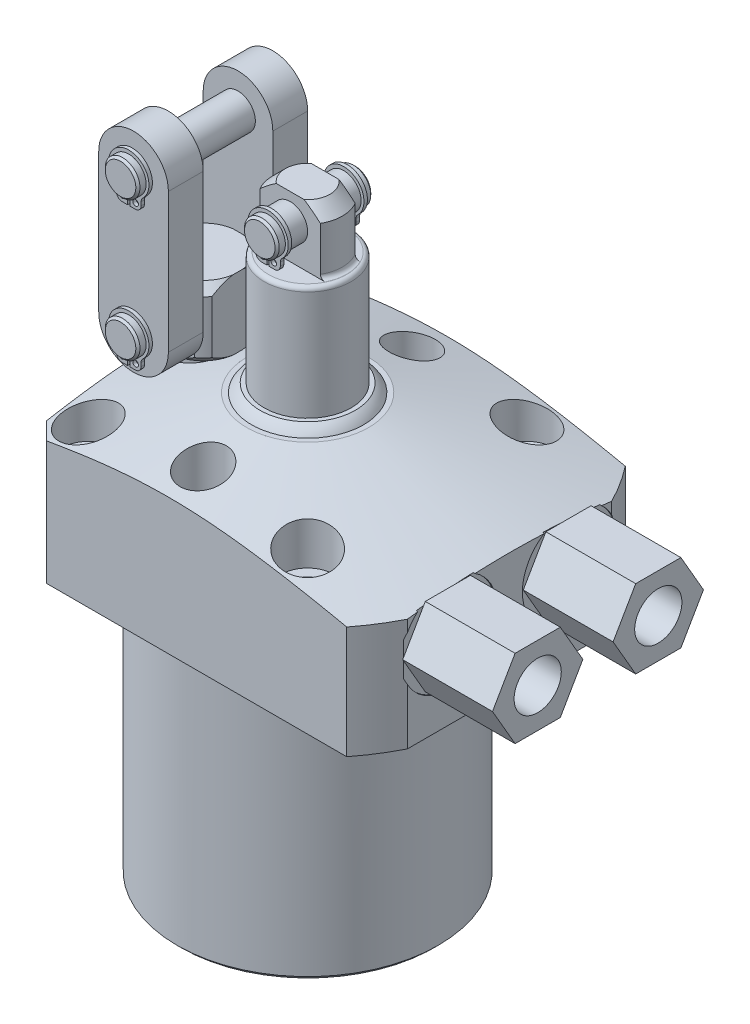
SolidWorks part; units mm, degrees
material "Alloy Steel"
ref_plane "Front Plane" through (0, 0, 0) normal (0, 0, 1) x (1, 0, 0)
ref_plane "Top Plane" through (0, 0, 0) normal (0, 1, 0) x (1, 0, 0)
ref_plane "Right Plane" through (0, 0, 0) normal (1, 0, 0) x (0, 0, -1)
sketch "Sketch28" plane through (0, 0, 0) normal (0, 0, 1) x (1, 0, 0)
  line L0 (0, 0) -> (0, 146.1857) construction
  line L1 (-11.1125, 28.575) -> (-41.275, 20.493)
  line L2 (-41.275, 20.493) -> (-41.275, 0)
  line L3 (-41.275, 0) -> (-23.8125, 0)
  line L6 (-23.8125, 0) -> (-23.8125, -47.625)
  line L9 (-23.8125, -47.625) -> (0, -47.625)
  line L10 (0, -47.625) -> (0, 28.575)
  line L11 (0, 28.575) -> (-11.1125, 28.575)
  dimension "D2" = 47.625
  dimension "D3" = 47.625
  dimension "D5" = 82.55
  dimension "D6" = 15
  dimension "D7" = 22.225
  dimension "D8" = 28.575
revolve "Revolve7" add sketch "Sketch28" angle 360 about L0
sketch "Sketch3" plane through (0, 28.575, 0) normal (0, 1, 0) x (-1, 0, 0)
  line L0 (25.4, -25.4) -> (-36.83, -25.4)
  line L3 (-36.83, 25.4) -> (25.4, 25.4)
  line L4 (25.4, -25.4) -> (25.4, 25.4)
  line L5 (-36.83, -25.4) -> (-36.83, 25.4)
  line L6 (-29.7523, 0) -> (31.3525, 0) construction
  dimension "D1" = 50.8
  dimension "D2" = 36.83
  dimension "D5" = 25.4
extrude "Cut-Extrude9" cut sketch "Sketch3" against normal up to next (76.2 mm away) flip side to cut
chamfer "Chamfer8" distance 3.175 angle 45 2 edges at (-25.4, 10.9638, -25.4) (-25.4, 10.9638, 25.4)
chamfer "Chamfer5" distance 0.762 angle 45 1 edges at (0, -47.625, -23.8125)
hole_wizard "Hole1" positions "Sketch32" profile "Sketch31" legacy
sketch "Sketch32" plane through (0, 28.575, 0) normal (0, 1, 0) x (-1, 0, 0)
  line L1 (0, 0) -> (-56.2722, 0) construction
  line L2 (0, 0) -> (0, 46.6984) construction
  point P11 (-20.0025, -20.0025)
  point P23 (-20.0025, 20.0025)
  point P25 (20.0025, -20.0025)
  point P26 (20.0025, 20.0025)
  dimension "D1" = 40.005
  dimension "D2" = 40.005
sketch "Sketch31" plane through (20.0025, 28.575, -20.0025) normal (1, 0, 0) x (0, 0, 1)
  line L0 (0, 0) -> (0, 28.575)
  line L1 (0, 28.575) -> (2.7813, 28.575)
  line L2 (2.7813, 28.575) -> (2.7813, 11.0998)
  line L3 (2.7813, 11.0998) -> (4.7625, 11.0998)
  line L4 (4.7625, 11.0998) -> (4.7625, 0)
  line L5 (4.7625, 0) -> (0, 0)
  line L6 (0, 110) -> (0, -10) construction
  dimension "Diameter" = 5.5626
  dimension "Depth" = 28.575
  dimension "C-Bore Diameter" = 9.525
  dimension "C-Bore Depth" = 11.0998
sketch "Sketch34" plane through (0, 28.575, 0) normal (0, 1, 0) x (1, 0, 0)
  line L0 (0, 0) -> (-28.6526, 0) construction
  circle A0 centre (0, 19.05) radius 4.2164
  circle A1 centre (0, -19.05) radius 4.2164
  circle A2 centre (0, 0) radius 19.05 construction
  circle A3 centre (-19.05, 0) radius 4.2164
  dimension "D1" = 8.4328
  dimension "D2" = 19.05
extrude "Cut-Extrude10" cut sketch "Sketch34" against normal blind 12.7
ref_plane "Plane23" through (0, 14.2748, 0) normal (0, -1, 0) x (1, 0, 0)
sketch "S2D0007" plane through (0, 14.2748, 0) normal (0, -1, 0) x (1, 0, 0)
  line L0 (36.83, -10.9982) -> (36.83, -19.6596)
  line L1 (36.83, -19.6596) -> (36.576, -19.6596)
  line L2 (36.576, -19.6596) -> (36.576, -15.5765)
  line L3 (36.576, -15.5765) -> (34.5059, -15.1365)
  line L4 (34.5059, -15.1365) -> (33.822, -14.4526)
  line L5 (33.822, -14.4526) -> (24.384, -14.4526)
  line L6 (24.384, -14.4526) -> (22.3084, -10.9982)
  line L7 (22.3084, -10.9982) -> (36.83, -10.9982)
  line L8 (-11.7468, -10.9982) -> (-12.1894, -10.9982) construction
  line L10 (36.83, -18.6327) -> (36.83, 18.6327) construction
  dimension "D1" = 9.1567
  dimension "D2" = 59
  dimension "D3" = 6.9088
  dimension "D4" = 45
  dimension "D5" = 12
  dimension "D6" = 2.0701
  dimension "D7" = 0.254
  dimension "D8" = 17.3228
  dimension "D9" = 10.9982
  dimension "D10" = 12.192
revolve "Cut-Revolve2" cut sketch "S2D0007" angle 360 about L8
ref_plane "Plane24" through (0, 0, -10.9982) normal (0, 0, 1) x (1, 0, 0)
sketch "Sketch6" plane through (0, 0, -10.9982) normal (0, 0, 1) x (1, 0, 0)
  line L0 (32.5341, 0) -> (-22.225, 0) construction
  line L1 (35.668, 0) -> (35.668, 1.4478)
  line L2 (35.668, 1.4478) -> (32.6075, 1.4478)
  line L3 (32.5341, 0) -> (36.83, 0) construction
  line L5 (29.9974, 0.5588) -> (31.1404, 0.5588)
  line L6 (29.9974, 0) -> (35.668, 0)
  line L8 (29.9974, 0.5588) -> (29.9974, 0)
  line L9 (29.9974, -21.0492) -> (29.9974, 0.6686) construction
  arc A1 (31.1404, 0.5588) -> (32.6075, 1.4478) centre (29.9974, 4.1) ccw
  dimension "D8" = 3.7211
  dimension "D1" = 1.4478
  dimension "D2" = 29.9974
  dimension "D7" = 0.5588
  dimension "D9" = 11.3411
  dimension "D10" = 2.286
revolve "Cut-Revolve3" cut sketch "Sketch6" angle 360 about L9
sketch "Sketch39" plane through (36.576, 0, 0) normal (1, 0, 0) x (0, 0, -1)
  line L1 (19.2398, 14.2748) -> (15.119, 21.4122)
  line L2 (15.119, 21.4122) -> (6.8774, 21.4122)
  line L3 (6.8774, 21.4122) -> (2.7566, 14.2748)
  line L4 (2.7566, 14.2748) -> (6.8774, 7.1374)
  line L5 (6.8774, 7.1374) -> (15.119, 7.1374)
  line L6 (15.119, 7.1374) -> (19.2398, 14.2748)
  circle A0 centre (10.9982, 14.2748) radius 7.1374 construction
  dimension "D1" = 14.2748
extrude "Extrude14" add sketch "Sketch39" along normal blind 16.383
hole_wizard "Hole2" positions "Sketch41" profile "Sketch40" legacy
sketch "Sketch41" plane through (52.959, 0, 0) normal (1, 0, 0) x (0, 0, -1)
  arc A0 (6.3827, 21.604) -> (19.1265, 11.283) centre (10.9982, 14.2748) ccw construction
  point P0 (10.9982, 14.2748)
sketch "Sketch40" plane through (52.959, 14.2748, -10.9982) normal (0, 1, 0) x (0, 0, -1)
  line L0 (0, 0) -> (0, 6.7056)
  line L1 (0, 6.7056) -> (4.3053, 6.7056)
  line L2 (4.3053, 6.7056) -> (4.3053, 0)
  line L3 (4.3053, 0) -> (0, 0)
  line L4 (0, 110) -> (0, -10) construction
  dimension "Diameter" = 8.6106
  dimension "Depth" = 6.7056
mirror "Mirror6" about plane through (0, 0, 0) normal (0, 0, 1) of "Hole2", "Extrude14", "Cut-Revolve2", "Cut-Revolve3"
sketch "Sketch33" plane through (0, 0, -10.9982) normal (0, 0, 1) x (1, 0, 0)
  line L0 (29.9974, 8.3297) -> (29.9974, -4.9597) construction
  line L1 (29.9974, 2.4904) -> (29.9974, -1.971) construction
  line L2 (24.3268, 1.4478) -> (35.668, 1.4478) construction
  circle A0 centre (25.2159, 0.5842) radius 0.889
  dimension "D3" = 1.778
  dimension "D1" = 9.5631
  dimension "D2" = 0.8636
revolve "Revolve9" add sketch "Sketch33" angle 360 about L0
mirror "Mirror7" about plane through (0, 0, 0) normal (0, 0, 1) of bodies 147
sketch "Sketch12" plane through (0, 0, 0) normal (0, 0, -1) x (-1, 0, 0)
  line L0 (0, 28.575) -> (0, 30.099)
  line L1 (0, 30.099) -> (8.6995, 30.099)
  line L2 (0, 28.575) -> (10.2235, 28.575)
  line L3 (0, 22.1056) -> (0, 27.6194) construction
  line L4 (11.1125, 28.575) -> (-11.1125, 28.575) construction
  arc A0 (10.2235, 28.575) -> (8.6995, 30.099) centre (6.1905, 26.066) ccw
  dimension "D1" = 4.7498
  dimension "D2" = 1.524
  dimension "D3" = 17.399
  dimension "D4" = 20.447
revolve "Revolve2" add sketch "Sketch12" angle 360 about L3
ref_plane "Plane25" through (0, 0, 0) normal (0, 0, 1) x (1, 0, 0)
sketch "Sketch13" plane through (0, 0, 0) normal (0, 0, 1) x (1, 0, 0)
  line L0 (0, 30.099) -> (0, 61.8998)
  line L1 (0, 61.8998) -> (4.064, 61.8998)
  line L2 (4.064, 61.8998) -> (6.35, 59.6138)
  line L3 (6.35, 50.8) -> (6.35, 59.6138)
  line L4 (7.9312, 30.099) -> (0, 30.099)
  line L5 (0, 23.0264) -> (0, 64.961) construction
  line L6 (-6.0362, 57.15) -> (17.7755, 57.15) construction
  line L7 (8.6995, 30.099) -> (-8.6995, 30.099) construction
  line L8 (32.5341, 0) -> (-22.225, 0) construction
  line L10 (6.35, 50.8) -> (7.9311, 50.8)
  line L11 (7.9311, 50.8) -> (7.9312, 30.099)
  dimension "D1" = 4.7498
  dimension "D2" = 57.15
  dimension "D3" = 12.7
  dimension "D4" = 45
  dimension "D5" = 2.286
  dimension "D6" = 15.8623
  dimension "D7" = 11.0998
revolve "Revolve3" add sketch "Sketch13" angle 360 about L5
sketch "Sketch14" plane through (0, 61.8998, 0) normal (0, 1, 0) x (-1, 0, 0)
  line L0 (-5.4993, 3.175) -> (5.4993, 3.175)
  line L2 (5.4993, -3.175) -> (-5.4993, -3.175)
  line L4 (0, 0) -> (-0.0035, 0) construction
  line L5 (34.2265, 0) -> (-34.2265, 0) construction
  circle A0 centre (0, 0) radius 6.35 construction
  arc A1 (5.4993, 3.175) -> (-5.4993, 3.175) centre (0, 0) ccw
  arc A2 (-5.4993, -3.175) -> (5.4993, -3.175) centre (0, 0) ccw
  dimension "D1" = 6.35
extrude "Cut-Extrude7" cut sketch "Sketch14" against normal up to surface (11.0998 mm away) up to face at (0, 50.8, -6.35)
fillet "Fillet4" radius 0.762 3 edges at (0, 50.8, -7.9311) (-6.35, 50.8, 0) (6.35, 50.8, 0)
sketch "Sketch29" plane through (0, 0, 0) normal (0, 0, 1) x (1, 0, 0)
  line L0 (-2.5368, 61.8998) -> (-4.064, 61.8998) construction
  circle A0 centre (0, 57.15) radius 3.1686
  dimension "D1" = 6.3373
  dimension "D2" = 4.7498
extrude "Extrude11" add sketch "Sketch29" along normal mid plane 17.4498
sketch "Sketch16" plane through (0, 52.3748, 8.7249) normal (0, 0, 1) x (1, 0, 0)
  line L0 (0.2083, 1.8616) -> (0.2083, -0.1704)
  line L1 (2.2403, 1.5036) -> (2.2403, 0.871)
  line L2 (1.1989, -0.1704) -> (0.2083, -0.1704)
  line L3 (-2.2403, 1.5036) -> (-2.2403, 0.871)
  line L4 (-1.1989, -0.1704) -> (-0.2083, -0.1704)
  line L5 (-0.2083, 1.8616) -> (-0.2083, -0.1704)
  line L6 (0, -3.8062) -> (0, 3.1748) construction
  arc A0 (0.2083, 1.8616) -> (-0.2083, 1.8616) centre (0, 4.7752) ccw
  arc A1 (2.5583, 2.2527) -> (-2.5583, 2.2527) centre (0, 4.9022) ccw
  arc A2 (2.5583, 2.2527) -> (2.2403, 1.5036) centre (3.2817, 1.5036) ccw
  arc A3 (1.1989, -0.1704) -> (2.2403, 0.871) centre (1.1989, 0.871) ccw
  circle A4 centre (1.0414, 0.871) radius 0.5207
  arc A5 (-2.5583, 2.2527) -> (-2.2403, 1.5036) centre (-3.2817, 1.5036) cw
  arc A6 (-1.1989, -0.1704) -> (-2.2403, 0.871) centre (-1.1989, 0.871) cw
  circle A7 centre (-1.0414, 0.871) radius 0.5207
  circle A8 centre (0, 4.7752) radius 3.1686 construction
  dimension "D1" = 3.683
  dimension "D4" = 1.0414
  dimension "D6" = 1.0414
  dimension "D7" = 2.032
  dimension "D8" = 2.921
  dimension "D10" = 1.0414
  dimension "D11" = 1.0414
  dimension "D2" = 2.032
  dimension "D3" = 0.127
  dimension "D5" = 1.0414
  dimension "D9" = 0.4166
extrude "Extrude2" add sketch "Sketch16" against normal blind 0.635 from offset 1.4986
chamfer "Chamfer6" distance 0.381 angle 45 2 edges at (3.1686, 57.15, -8.7249) (3.1686, 57.15, 8.7249)
mirror "Mirror2" about plane through (0, 0, 0) normal (0, 0, 1) of "Extrude2"
sketch "Sketch35" plane through (0, 0, 0) normal (0, 0, 1) x (1, 0, 0)
  line L0 (-19.05, 43.5741) -> (-19.05, 11.6793) construction
  line L1 (-19.05, 15.875) -> (-14.2875, 15.875)
  line L2 (-14.2875, 15.875) -> (-14.2875, 28.575)
  line L3 (-14.2875, 28.575) -> (-12.6365, 28.575)
  line L4 (-11.1125, 30.099) -> (-11.1125, 39.751)
  line L5 (-12.6365, 41.275) -> (-19.05, 41.275)
  line L6 (-19.05, 41.275) -> (-19.05, 15.875)
  line L7 (11.1125, 28.575) -> (-11.1125, 28.575) construction
  line L8 (-11.1125, 39.751) -> (-12.6365, 41.275)
  line L9 (-12.6365, 28.575) -> (-11.1125, 30.099)
  point P6 (-11.1125, 28.575)
  point P7 (-11.1125, 41.275)
  dimension "D1" = 12.7
  dimension "D2" = 9.525
  dimension "D3" = 15.875
  dimension "D4" = 25.4
  dimension "D5" = 12.7
  dimension "D6" = 19.05
  dimension "D9" = 1.524
  dimension "D10" = 1.524
revolve "Revolve10" add sketch "Sketch35" angle 360 about L0
sketch "Sketch36" plane through (0, 41.275, 0) normal (0, 1, 0) x (1, 0, 0)
  line L0 (-19.05, 0) -> (-19.05, 19.05) construction
  line L1 (-23.8125, 6.35) -> (-14.2875, 6.35)
  line L2 (-25.4, 4.7625) -> (-25.4, -4.7625)
  line L3 (-23.8125, -6.35) -> (-14.2875, -6.35)
  line L4 (-12.7, 4.7625) -> (-12.7, -4.7625)
  line L5 (-19.05, 0) -> (0, 0) construction
  line L6 (-34.2265, 0) -> (34.2265, 0) construction
  circle A0 centre (-19.05, 0) radius 7.9375 construction
  arc A2 (-25.4, 4.7625) -> (-25.4, -4.7625) centre (-19.05, 0) ccw
  arc A3 (-23.8125, -6.35) -> (-14.2875, -6.35) centre (-19.05, 0) ccw
  arc A4 (-14.2875, 6.35) -> (-23.8125, 6.35) centre (-19.05, 0) ccw
  arc A5 (-12.7, -4.7625) -> (-12.7, 4.7625) centre (-19.05, 0) ccw
  dimension "D1" = 12.7
  dimension "D2" = 12.7
extrude "Cut-Extrude11" cut sketch "Sketch36" against normal up to surface (12.7 mm away) up to face at (-25.4635, 28.575, 0)
sketch "Sketch30" plane through (0, 0, 0) normal (0, 0, 1) x (1, 0, 0)
  line L0 (-41.275, 0) -> (-32.5341, 0) construction
  circle A0 centre (-19.05, 34.925) radius 3.1686
  dimension "D3" = 6.3373
  dimension "D1" = 34.925
  dimension "D2" = 19.05
extrude "Extrude12" add sketch "Sketch30" along normal mid plane 30.1498
sketch "Sketch19" plane through (-22.225, 11.0998, 15.0749) normal (0, 0, 1) x (1, 0, 0)
  line L0 (3.3833, 20.9116) -> (3.3833, 18.8796)
  line L1 (5.4153, 20.5536) -> (5.4153, 19.921)
  line L2 (4.3739, 18.8796) -> (3.3833, 18.8796)
  line L3 (0.9347, 20.5536) -> (0.9347, 19.921)
  line L4 (1.9761, 18.8796) -> (2.9667, 18.8796)
  line L5 (2.9667, 20.9116) -> (2.9667, 18.8796)
  line L6 (3.175, -5.3833) -> (3.175, 4.2478) construction
  arc A0 (3.3833, 20.9116) -> (2.9667, 20.9116) centre (3.175, 23.8252) ccw
  arc A1 (5.7333, 21.3027) -> (0.6167, 21.3027) centre (3.175, 23.9522) ccw
  arc A2 (5.7333, 21.3027) -> (5.4153, 20.5536) centre (6.4567, 20.5536) ccw
  arc A3 (4.3739, 18.8796) -> (5.4153, 19.921) centre (4.3739, 19.921) ccw
  circle A4 centre (4.4247, 19.921) radius 0.5207
  arc A5 (0.6167, 21.3027) -> (0.9347, 20.5536) centre (-0.1067, 20.5536) cw
  arc A6 (1.9761, 18.8796) -> (0.9347, 19.921) centre (1.9761, 19.921) cw
  circle A7 centre (1.9253, 19.921) radius 0.5207
  circle A8 centre (3.175, 23.8252) radius 3.1686 construction
  dimension "D1" = 3.683
  dimension "D3" = 0.127
  dimension "D4" = 1.0414
  dimension "D5" = 1.0414
  dimension "D6" = 1.0414
  dimension "D9" = 2.921
  dimension "D2" = 2.032
  dimension "D7" = 0.4166
  dimension "D8" = 2.032
  dimension "D10" = 1.0414
  dimension "D11" = 1.0414
extrude "Extrude4" add sketch "Sketch19" against normal blind 0.635 from offset 1.4986
sketch "Sketch37" plane through (0, 0, 6.35) normal (0, 0, 1) x (1, 0, 0)
  line L0 (-25.4, 60.325) -> (-25.4, 34.925)
  line L1 (-12.7, 60.325) -> (-12.7, 34.925)
  arc A0 (-12.7, 60.325) -> (-25.4, 60.325) centre (-19.05, 60.325) ccw
  arc A1 (-25.4, 34.925) -> (-12.7, 34.925) centre (-19.05, 34.925) ccw
  dimension "D1" = 12.7
  dimension "D2" = 25.4
  dimension "D3" = 19.3128
extrude "Extrude13" add sketch "Sketch37" along normal blind 6.35
mirror "Mirror3" about plane through (0, 0, 0) normal (0, 0, 1) of "Extrude4"
chamfer "Chamfer7" distance 0.381 angle 45 2 edges at (-15.8814, 34.925, -15.0749) (-15.8814, 34.925, 15.0749)
pattern_linear "LPattern2" count 2 spacing 25.4 along (0, 1, 0) of "Extrude4", "Mirror3", "Chamfer7", "Extrude12"
mirror "Mirror8" about plane through (0, 0, 0) normal (0, 0, 1) of "Extrude13"
